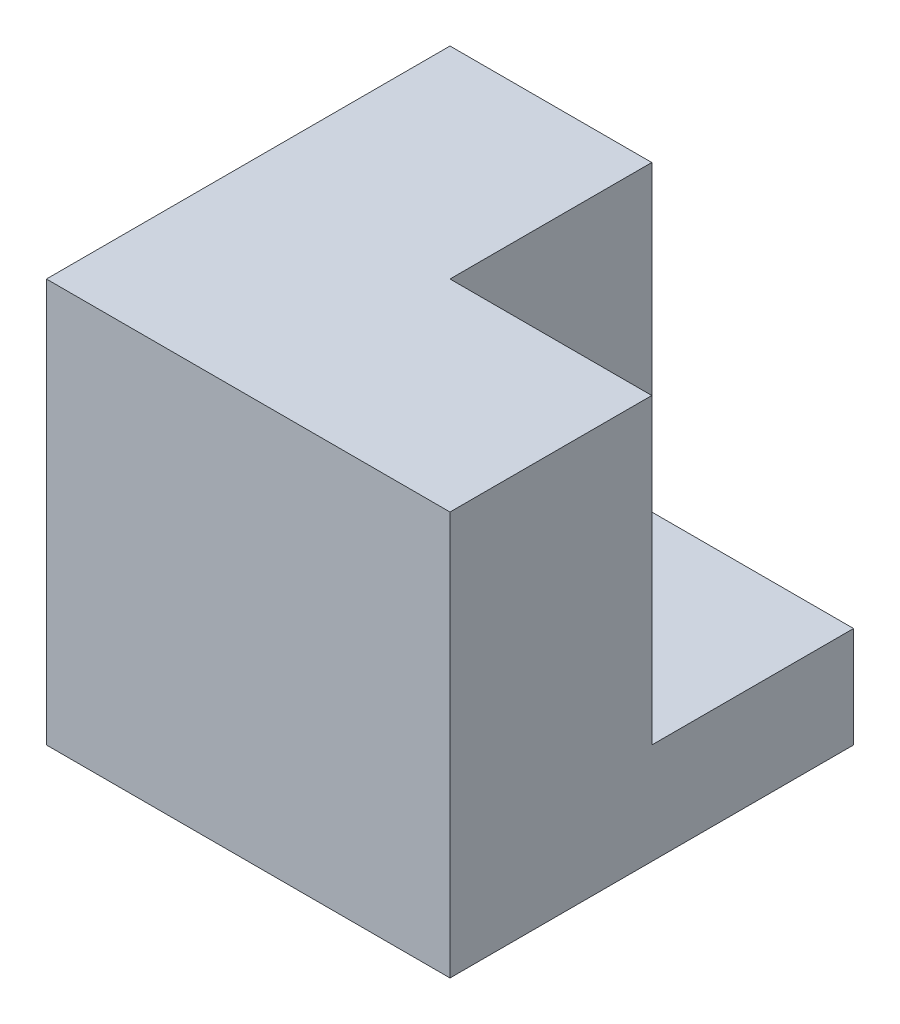
SolidWorks part; units mm, degrees
ref_plane "Front Plane" through (0, 0, 0) normal (0, 0, 1) x (1, 0, 0)
ref_plane "Top Plane" through (0, 0, 0) normal (0, 1, 0) x (1, 0, 0)
ref_plane "Right Plane" through (0, 0, 0) normal (1, 0, 0) x (0, 0, -1)
sketch "Sketch1" plane through (0, 0, 0) normal (0, 0, 1) x (1, 0, 0)
  line L1 (0, 0) -> (76.2, 0)
  line L2 (0, 0) -> (0, 76.2)
  line L3 (0, 76.2) -> (76.2, 76.2)
  line L4 (76.2, 0) -> (76.2, 76.2)
  dimension "D1" = 76.2
extrude "Boss-Extrude1" add sketch "Sketch1" along normal blind 76.2
sketch "Sketch2" plane through (76.2, 0, 0) normal (1, 0, 0) x (0, 0, -1)
  line L0 (-76.2, 0) -> (0, 0) construction
  line L1 (0, 76.2) -> (-38.1, 76.2)
  line L2 (0, 76.2) -> (0, 19.05)
  line L3 (0, 19.05) -> (-38.1, 19.05)
  line L4 (-38.1, 76.2) -> (-38.1, 19.05)
  dimension "D1" = 19.05
  dimension "D2" = 38.1
extrude "Cut-Extrude1" cut sketch "Sketch2" against normal blind 38.1
